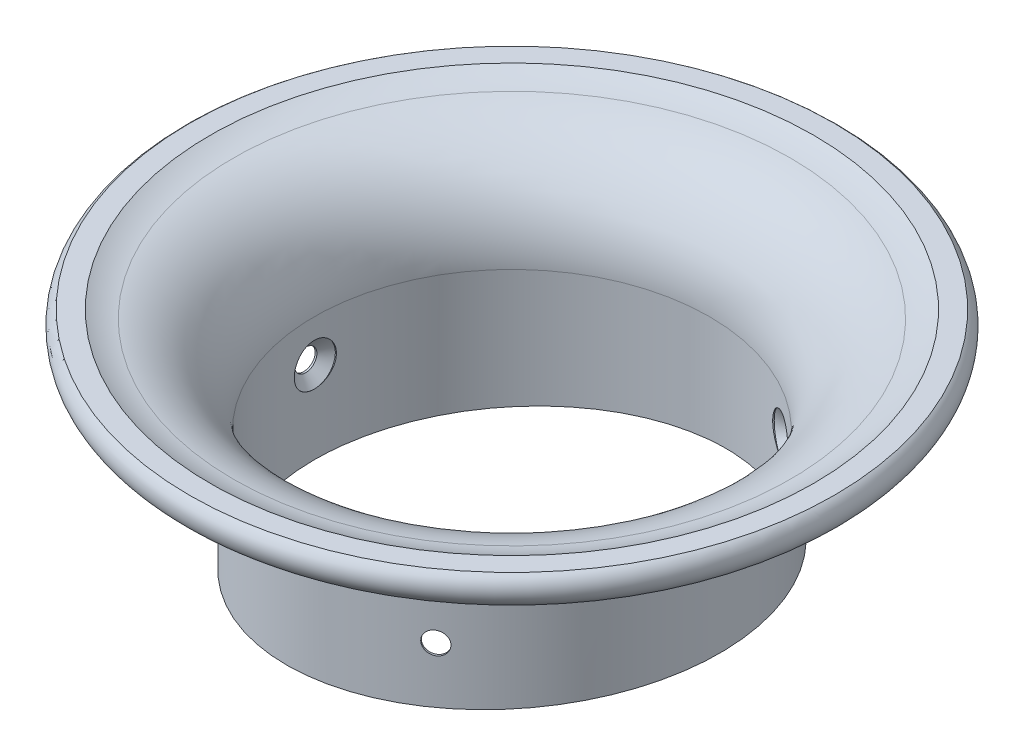
SolidWorks part; units mm, degrees
ref_plane "Front Plane" through (0, 0, 0) normal (0, 0, 1) x (1, 0, 0)
ref_plane "Top Plane" through (0, 0, 0) normal (0, 1, 0) x (1, 0, 0)
ref_plane "Right Plane" through (0, 0, 0) normal (1, 0, 0) x (0, 0, -1)
sketch "Sketch1" plane through (0, 0, 0) normal (0, 0, 1) x (1, 0, 0)
  line L13 (0, -32.9325) -> (0, 32.9325) construction
  line L14 (0, -32.9325) -> (-60.325, -32.9325) construction
  line L16 (-60.325, -32.9325) -> (-60.325, 5.3493)
  line L17 (-60.325, -32.9325) -> (-63.5, -32.9325)
  line L18 (-63.5, -32.9325) -> (-63.5, 2.1743)
  line L22 (-63.5, 2.1743) -> (-66.675, 2.1743)
  line L23 (-66.675, 5.3493) -> (-66.675, 2.1743)
  line L26 (-80.5158, 32.9325) -> (-86.8658, 32.9325)
  line L28 (0, 32.9325) -> (-86.8658, 32.9325) construction
  arc A2 (-60.325, 5.3493) -> (-79.4176, 32.7365) centre (-89.514, 5.3493) ccw
  arc A3 (-66.675, 5.3493) -> (-86.8658, 28.0342) centre (-89.514, 5.3493) ccw
  arc A4 (-86.8658, 32.9325) -> (-86.8658, 28.0342) centre (-86.4912, 30.4833) ccw
  arc A8 (-60.325, 5.3493) -> (-86.1295, 34.3414) centre (-89.514, 5.3493) ccw construction
  arc A9 (-79.4176, 32.7365) -> (-80.5158, 32.9325) centre (-80.5158, 29.7575) ccw
  point P3 (0, 0)
  dimension "D8" = 3.175
  dimension "D9" = 22.839
  dimension "D10" = 2.4776
  dimension "D3" = 3.175
  dimension "D4" = 35.1068
  dimension "D6" = 6.35
  dimension "D7" = 6.35
  dimension "D11" = 25.8599
sketch "Sketch2" plane through (0, 0, 0) normal (0, 0, 1) x (1, 0, 0)
  line L0 (0, 0) -> (0, 25.4) construction
  line L1 (0, 0) -> (-25.4, 0) construction
  line L2 (-25.4, 0) -> (-25.4, 25.4) construction
  line L3 (-25.4, 30.1625) -> (-25.4, 25.4) construction
  line L4 (-25.4, 27.7812) -> (-30.1625, 27.7812) construction
  line L5 (0, 0) -> (1.5875, 0)
  line L6 (1.5875, 0) -> (1.5875, -38.1)
  line L7 (1.5875, -38.1) -> (4.7625, -38.1)
  line L8 (4.7625, -38.1) -> (4.7625, 0)
  line L9 (1.5875, -38.1) -> (65.0875, -38.1) construction
  line L10 (65.0875, -38.1) -> (65.0875, 33.1059) construction
  line L11 (-30.1625, 33.1059) -> (65.0875, 33.1059) construction
  arc A0 (0, 0) -> (-25.4, 25.4) centre (-25.4, 0) ccw
  arc A1 (4.7625, 0) -> (-25.4, 30.1625) centre (-25.4, 0) ccw
  arc A2 (-25.4, 30.1625) -> (-25.4, 25.4) centre (-30.1625, 27.7812) ccw
  arc A3 (-25.4, 25.4) -> (-25.4, 30.1625) centre (-30.1625, 27.7812) ccw construction
  dimension "D1" = 25.4
  dimension "D3" = 4.7625
  dimension "D4" = 38.1
  dimension "D5" = 3.175
  dimension "D6" = 127
  dimension "D2" = 4.7625
revolve "RevolvedVenturi-5inchOutsideDiaLower_2inchDeep" add sketch "Sketch2" angle 360 about L10
sketch "Sketch3" plane through (0, 0, 0) normal (0, 0, 1) x (1, 0, 0)
  line L0 (1.5875, -38.1) -> (128.5875, -38.1) construction
  line L1 (128.5875, -38.1) -> (305.2706, -38.1) construction
  line L2 (305.2706, -38.1) -> (305.2706, -11.5312) construction
  line L3 (305.2706, -11.5312) -> (1.5875, -38.1)
  line L4 (1.5875, -38.1) -> (5.8933, -87.316)
  line L5 (5.8933, -87.316) -> (309.5764, -60.7472)
  line L6 (309.5764, -60.7472) -> (305.2706, -11.5312)
  point P5 (1.5875, -38.1)
  dimension "D1" = 85
extrude "Cut-Extrude1" cut sketch "Sketch3" against normal through all both and the other way through all
hole_wizard "CSK for 1/4 Flat Head Machine Screw (100)1" positions "3DSketch1" profile "Sketch5" countersink size "1/4" standard "ANSI Inch" end condition up to next
sketch3d "3DSketch1"
  line L0 (65.0875, 0, 0) -> (4.7625, 0, 0) construction
  line L2 (4.7625, 0, 0) -> (4.7625, -12.7, 0) construction
  circle A0 centre (65.0875, 0, 0) radius 60.325 construction
  point P5 (65.0875, -60.325, 0)
  point P12 (4.7625, -12.7, 0)
  point P16 (4.7625, -12.7, 0)
  point P18 (4.7625, -12.7, 0)
  point P22 (4.7625, -12.7, 0)
  dimension "D1" = 12.7
sketch "Sketch5" plane through (4.7625, -12.7, 0) normal (0, 1, 0) x (0, 0, -1)
  line L0 (0, 0) -> (0, 26.419)
  line L1 (0, 26.419) -> (3.3782, 26.419)
  line L2 (3.3782, 26.419) -> (3.3782, 2.5682)
  line L3 (3.3782, 2.5682) -> (6.4389, 0)
  line L5 (6.4389, 0) -> (0, 0)
  line L6 (-3.3782, 2.5682) -> (-6.4389, 0) construction
  line L11 (0, -6.35) -> (0, 107.95) construction
  dimension "Thru Hole Dia." = 6.7564
  dimension "Thru Hole Depth" = 26.419
  dimension "Near C'Sink Dia." = 12.8778
  dimension "Near C'Sink Angle" = 100
pattern_circular "CirPattern1" count 3 over 360 about axis through (65.0875, 0, 0) along (0, -1, 0) of "CSK for 1/4 Flat Head Machine Screw (100)1"
fillet "Fillet1" radius 25.4 1 edges at (65.0875, 30.1625, -90.4875)
sketch "Sketch6" plane through (0, 0, 0) normal (0, 0, 1) x (1, 0, 0)
  line L0 (0, 0) -> (139.3265, 0) construction
  line L1 (69.6632, 0) -> (69.6632, 53.3082) construction
  line L3 (183.9632, 74.5067) -> (-44.6368, 74.5067)
  line L4 (183.9632, 74.5067) -> (183.9632, 32.1098)
  line L5 (183.9632, 32.1098) -> (-44.6368, 32.1098)
  line L6 (-44.6368, 74.5067) -> (-44.6368, 32.1098)
  line L7 (183.9632, 74.5067) -> (-44.6368, 32.1098) construction
  line L8 (183.9632, 32.1098) -> (-44.6368, 74.5067) construction
  dimension "D1" = 228.6
  dimension "D2" = 53.3082
extrude "Cut-Extrude2" cut sketch "Sketch6" against normal through all both and the other way through all
